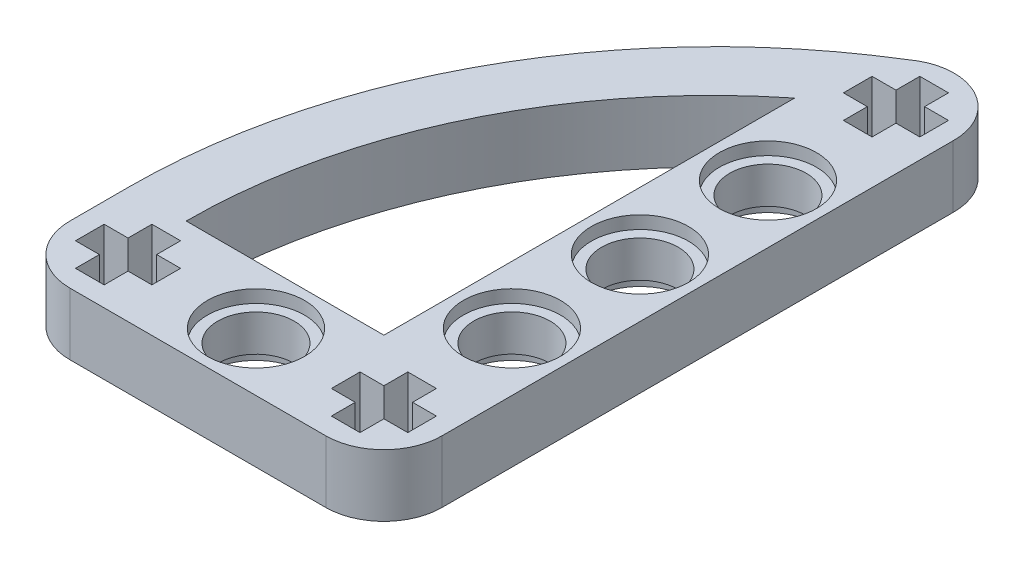
SolidWorks part; units mm, degrees
ref_plane "Front Plane" through (0, 0, 0) normal (0, 0, 1) x (1, 0, 0)
ref_plane "Top Plane" through (0, 0, 0) normal (0, 1, 0) x (1, 0, 0)
ref_plane "Right Plane" through (0, 0, 0) normal (1, 0, 0) x (0, 0, -1)
sketch "Sketch1" plane through (0, 0, 0) normal (0, 1, 0) x (1, 0, 0)
  line L0 (-8.0301, 0) -> (8.0399, 0) construction
  line L1 (-55, 0) -> (55, 0) construction
  line L2 (-8.0258, 3.65) -> (4.3899, 3.65)
  line L3 (-8.0301, -3.65) -> (8.0399, -3.65)
  line L4 (8.0399, 0) -> (8.0399, 32.16) construction
  line L5 (4.3899, 3.65) -> (4.3899, 29.4436)
  line L6 (11.6899, 0) -> (11.6899, 32.1)
  line L7 (-11.6801, 0) -> (-11.6801, 3.7106)
  line L8 (-8.9301, 0.9) -> (-10.4301, 0.9)
  line L9 (-5.6301, -0.9) -> (-7.1301, -0.9)
  line L10 (-5.6301, -0.9) -> (-5.6301, 0.9)
  line L11 (-5.6301, 0.9) -> (-7.1301, 0.9)
  line L12 (-10.4301, -0.9) -> (-10.4301, 0.9)
  line L13 (-5.6301, -0.9) -> (-10.4301, 0.9) construction
  line L14 (-5.6301, 0.9) -> (-10.4301, -0.9) construction
  line L15 (10.4399, -0.9) -> (8.9399, -0.9)
  line L16 (10.4399, -0.9) -> (10.4399, 0.9)
  line L17 (10.4399, 0.9) -> (8.9399, 0.9)
  line L18 (5.6399, -0.9) -> (5.6399, 0.9)
  line L19 (10.4399, -0.9) -> (5.6399, 0.9) construction
  line L20 (10.4399, 0.9) -> (5.6399, -0.9) construction
  line L21 (5.6399, 33.06) -> (7.1399, 33.06)
  line L22 (5.6399, 33.06) -> (5.6399, 31.26)
  line L23 (5.6399, 31.26) -> (7.1399, 31.26)
  line L24 (10.4399, 33.06) -> (10.4399, 31.26)
  line L25 (5.6399, 33.06) -> (10.4399, 31.26) construction
  line L26 (5.6399, 31.26) -> (10.4399, 33.06) construction
  line L27 (-8.9301, -2.4) -> (-7.1301, -2.4)
  line L28 (-8.9301, -2.4) -> (-8.9301, -0.9)
  line L29 (-8.9301, 2.4) -> (-7.1301, 2.4)
  line L30 (-7.1301, -2.4) -> (-7.1301, -0.9)
  line L31 (-8.9301, -2.4) -> (-7.1301, 2.4) construction
  line L32 (-8.9301, 2.4) -> (-7.1301, -2.4) construction
  line L33 (7.1399, 2.4) -> (8.9399, 2.4)
  line L34 (7.1399, 2.4) -> (7.1399, 0.9)
  line L35 (7.1399, -2.4) -> (8.9399, -2.4)
  line L36 (8.9399, 2.4) -> (8.9399, 0.9)
  line L37 (7.1399, 2.4) -> (8.9399, -2.4) construction
  line L38 (7.1399, -2.4) -> (8.9399, 2.4) construction
  line L39 (7.1399, 29.76) -> (8.9399, 29.76)
  line L40 (7.1399, 29.76) -> (7.1399, 31.26)
  line L41 (7.1399, 34.56) -> (8.9399, 34.56)
  line L42 (8.9399, 29.76) -> (8.9399, 31.26)
  line L43 (7.1399, 29.76) -> (8.9399, 34.56) construction
  line L44 (7.1399, 34.56) -> (8.9399, 29.76) construction
  line L45 (-8.9301, 0.9) -> (-8.9301, 2.4)
  line L46 (-8.9301, -0.9) -> (-10.4301, -0.9)
  line L47 (8.9399, -0.9) -> (8.9399, -2.4)
  line L48 (-7.1301, 0.9) -> (-7.1301, 2.4)
  line L49 (7.1399, -0.9) -> (7.1399, -2.4)
  line L50 (7.1399, 0.9) -> (5.6399, 0.9)
  line L51 (7.1399, -0.9) -> (5.6399, -0.9)
  line L52 (8.9399, 33.06) -> (10.4399, 33.06)
  line L53 (7.1399, 33.06) -> (7.1399, 34.56)
  line L54 (8.9399, 33.06) -> (8.9399, 34.56)
  line L55 (8.9399, 31.26) -> (10.4399, 31.26)
  line L56 (4.3899, 8.04) -> (18.1412, 8.04) construction
  line L57 (4.3899, 16.08) -> (21.1456, 16.08) construction
  line L58 (4.3899, 24.12) -> (23.7377, 24.12) construction
  arc A0 (-11.6801, 0) -> (-8.0301, -3.65) centre (-8.0301, 0) ccw
  arc A1 (8.0399, -3.65) -> (11.6899, 0) centre (8.0399, 0) ccw
  arc A3 (11.6899, 32.1) -> (5.8622, 35.0898) centre (8.0399, 32.16) ccw
  arc A6 (-11.6801, 3.7106) -> (5.8622, 35.0898) centre (25.1562, 3.7106) cw
  arc A7 (-8.0258, 3.65) -> (4.3899, 29.4436) centre (24.9679, 3.6535) cw
  circle A8 centre (0.0049, 0) radius 2.4
  circle A12 centre (8.0399, 24.12) radius 2.4
  circle A13 centre (8.0399, 16.08) radius 2.4
  circle A14 centre (8.0399, 8.04) radius 2.4
  point P5 (0.0049, 0)
  point P12 (8.0399, 16.05)
  point P21 (-5.5335, 24.0836)
  point P22 (-2.5141, 21.9106)
  dimension "D5" = 3.72
  dimension "D4" = 8.04
  dimension "D6" = 8.04
  dimension "D8" = 8.04
  dimension "D1" = 7.3
  dimension "D2" = 8.035
  dimension "D3" = 7.3
  dimension "D7" = 8.04
  dimension "D9" = 8.035
extrude "Boss-Extrude3" add sketch "Sketch1" along normal blind 3.9
sketch "Sketch3" plane through (0, 3.9, 0) normal (0, 1, 0) x (1, 0, 0)
  circle A0 centre (0.0049, 0) radius 3.05
  circle A1 centre (8.0399, 8.04) radius 3.05
  circle A2 centre (8.0399, 16.08) radius 3.05
  circle A3 centre (8.0399, 24.12) radius 3.05
extrude "Cut-Extrude16" cut sketch "Sketch3" against normal blind 0.8
sketch "Sketch4" plane through (0, 0, 0) normal (0, -1, 0) x (1, 0, 0)
  circle A0 centre (0, 0) radius 3.05
  circle A1 centre (8.0399, -8.04) radius 3.05
  circle A2 centre (8.0399, -16.08) radius 3.05
  circle A3 centre (8.0399, -24.12) radius 3.05
extrude "Cut-Extrude17" cut sketch "Sketch4" against normal blind 0.8
